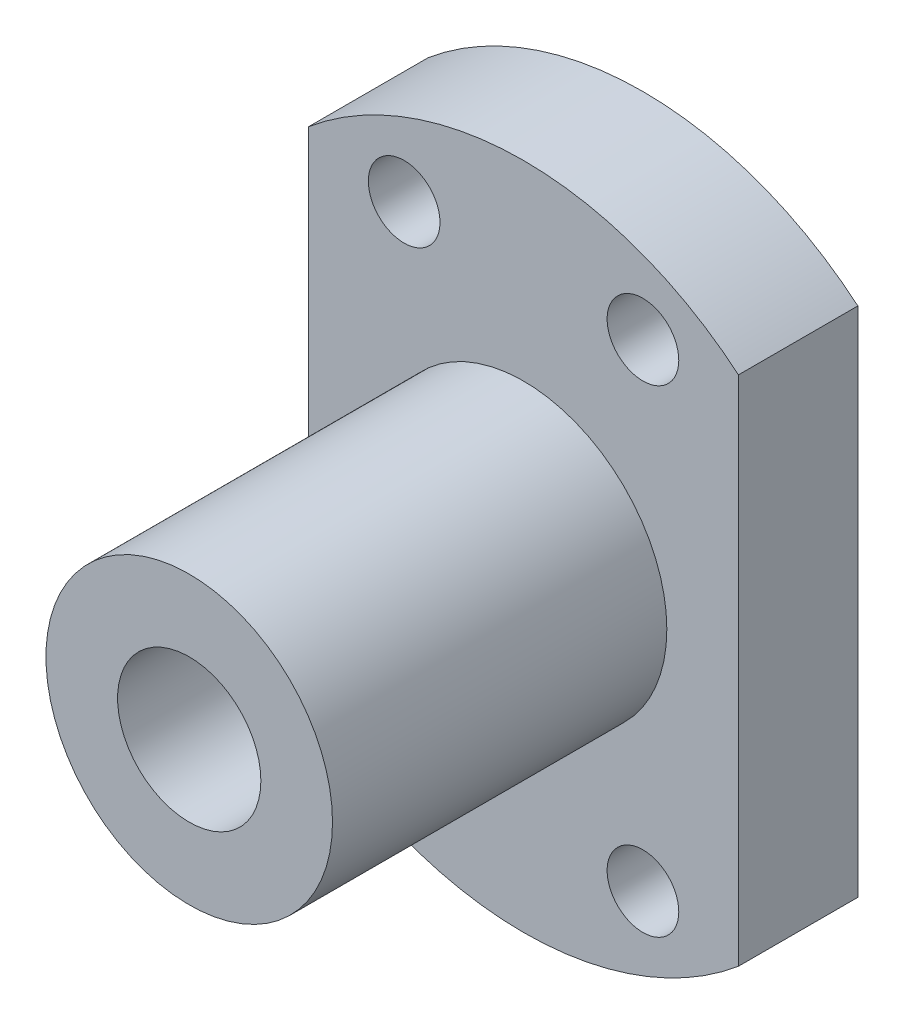
SolidWorks part; units mm, degrees
ref_plane "Front Plane" through (0, 0, 0) normal (0, 0, 1) x (1, 0, 0)
ref_plane "Top Plane" through (0, 0, 0) normal (0, 1, 0) x (1, 0, 0)
ref_plane "Right Plane" through (0, 0, 0) normal (1, 0, 0) x (0, 0, -1)
sketch "Sketch1" plane through (0, 0, 0) normal (0, 0, 1) x (1, 0, 0)
  line L0 (-9, 10.7238) -> (-9, -10.7238)
  line L1 (9, 10.7238) -> (9, -10.7238)
  line L2 (-9, 0) -> (9, 0) construction
  line L3 (-5, 10) -> (5, -10) construction
  line L4 (-5, -10) -> (5, 10) construction
  arc A0 (9, 10.7238) -> (-9, 10.7238) centre (0, 0) ccw
  arc A1 (-9, -10.7238) -> (9, -10.7238) centre (0, 0) ccw
  circle A2 centre (0, 0) radius 3
  circle A3 centre (-5, 10) radius 1.5
  circle A4 centre (5, 10) radius 1.5
  circle A5 centre (-5, -10) radius 1.5
  circle A6 centre (5, -10) radius 1.5
  point P7 (0, 0)
  point P18 (0, 0)
  dimension "D2" = 14
  dimension "D3" = 6
  dimension "D6" = 3
  dimension "D1" = 18
  dimension "D4" = 20
  dimension "D5" = 10
extrude "Boss-Extrude1" add sketch "Sketch1" along normal blind 5
sketch "Sketch2" plane through (0, 0, 5) normal (0, 0, 1) x (1, 0, 0)
  circle A0 centre (0, 0) radius 6
  circle A1 centre (0, 0) radius 3
  circle A2 centre (0, 0) radius 3 construction
  dimension "D1" = 12
extrude "Boss-Extrude2" add sketch "Sketch2" along normal blind 14
